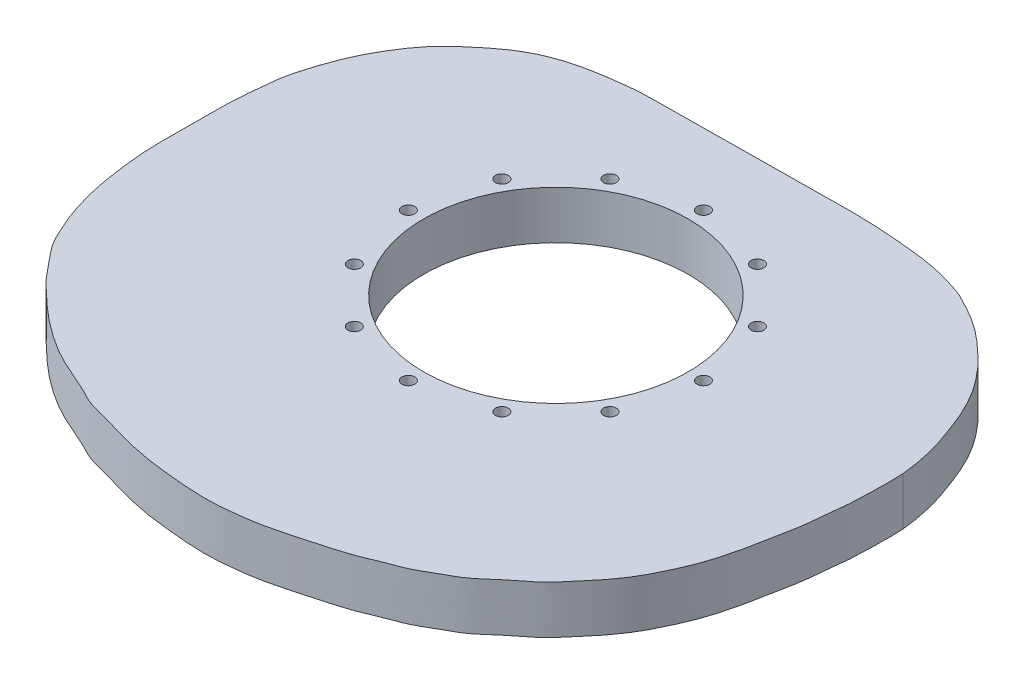
SolidWorks part; units mm, degrees
material "PC High Viscosity"
ref_plane "Front Plane" through (0, 0, 0) normal (0, 0, 1) x (1, 0, 0)
ref_plane "Top Plane" through (0, 0, 0) normal (0, 1, 0) x (1, 0, 0)
ref_plane "Right Plane" through (0, 0, 0) normal (1, 0, 0) x (0, 0, -1)
ref_plane "Plane1" through (0, -5, 0) normal (0, -1, 0) x (1, 0, 0)
sketch "Sketch1" plane through (0, -5, 0) normal (0, -1, 0) x (1, 0, 0)
  line L0 (-553.4146, 21.431) -> (-553.4146, 113.672) construction
  line L1 (-553.4146, 21.431) -> (-453.7553, 21.431) construction
  circle A0 centre (-640.9481, 175.1125) radius 4.5 construction
  circle A1 centre (-701.6642, 122.5526) radius 4.5 construction
  circle A2 centre (-720.0364, 42.0554) radius 4.5 construction
  circle A3 centre (-703.4746, -33.9322) radius 4.5 construction
  circle A4 centre (-640.0771, -82.4235) radius 4.5 construction
  circle A5 centre (-550.8446, -84.6039) radius 4.5 construction
  circle A6 centre (-463.1234, -82.9904) radius 4.5 construction
  circle A7 centre (-402.2158, -32.3116) radius 4.5 construction
  circle A8 centre (-390.2401, 53.8738) radius 4.5 construction
  circle A9 centre (-420.5023, 130.1207) radius 4.5 construction
  circle A10 centre (-489.4438, 179.9192) radius 4.5 construction
  circle A11 centre (-561.1968, 193.8588) radius 4.5 construction
  circle A12 centre (-553.4146, 21.431) radius 85 construction
  circle A13 centre (-553.4146, 21.431) radius 70.0278
  circle A14 centre (-553.4146, 21.431) radius 78.0278 construction
  circle A15 centre (-553.4146, -56.5968) radius 3.175 construction
  circle A16 centre (-592.4285, -46.143) radius 3.175 construction
  circle A17 centre (-620.9886, -17.5829) radius 3.175 construction
  circle A18 centre (-631.4424, 21.431) radius 3.175 construction
  circle A19 centre (-620.9886, 60.4449) radius 3.175 construction
  circle A20 centre (-592.4285, 89.0051) radius 3.175 construction
  circle A21 centre (-553.4146, 99.4588) radius 3.175 construction
  circle A22 centre (-514.4007, 89.0051) radius 3.175 construction
  circle A23 centre (-485.8405, 60.4449) radius 3.175 construction
  circle A24 centre (-475.3868, 21.431) radius 3.175 construction
  circle A25 centre (-485.8405, -17.5829) radius 3.175 construction
  circle A26 centre (-514.4007, -46.143) radius 3.175 construction
  circle A27 centre (-553.4146, 143.3336) radius 10 construction
  spline S0 degree 3 poles (-380.0492, 11.3845) (-380.3517, 7.6228) (-381.6942, -0.7552) (-384.4462, -11.6637) (-388.1031, -21.3921) (-391.9257, -31.5758) (-398.2955, -43.9247) (-407.1289, -55.652) (-416.3823, -64.7215) (-428.7027, -75.72) (-441.7653, -82.663) (-448.7361, -86.4746) (-459.3782, -89.3832) (-468.64, -91.8901) (-483.8831, -93.5312) (-505.2938, -95.3605) (-537.9356, -94.81) (-620.864, -94.0649) (-625.2898, -93.7427) (-632.6167, -93.1087) (-643.9696, -91.505) (-654.6984, -89.3136) (-665.5537, -85.8204) (-677.5449, -79.6796) (-689.8218, -69.7893) (-700.8189, -59.8464) (-709.7194, -47.179) (-717.4544, -32.8609) (-722.9168, -16.9365) (-725.8708, -5.4697) (-726.4326, 2.7477) (-728.0614, 15.9524) (-728.0166, 29.622) (-728.1832, 51.3785) (-728.2105, 66.1658) (-725.0161, 91.653) (-719.3074, 111.76) (-715.0325, 120.9389) (-713.403, 124.3556) knots 0.505449 0.505449 0.505449 0.505449 0.517879 0.529901 0.541289 0.553 0.566304 0.579903 0.592751 0.607328 0.620921 0.630996 0.642558 0.653666 0.667425 0.683271 0.705284 0.737162 0.74462 0.753697 0.76593 0.777787 0.789713 0.802766 0.81692 0.830645 0.844558 0.85902 0.87372 0.885805 0.895976 0.908692 0.922196 0.938566 0.952559 0.970499 0.987058 1 1 1 1
  spline S1 degree 3 poles (-713.403, 124.3556) (-712.0821, 127.125) (-709.6174, 132.1606) (-702.1703, 140.5425) (-695.5252, 149.3502) (-687.2231, 156.81) (-678.2069, 165.4785) (-664.3825, 175.5745) (-651.5938, 182.9116) (-634.0958, 189.8974) (-627.7186, 194.1731) (-612.1137, 197.5774) (-603.1302, 200.7835) (-587.8782, 204.2739) (-575.4184, 205.6622) (-564.4048, 206.8324) (-549.9761, 207.4282) (-539.5697, 206.291) (-527.523, 204.923) (-512.5859, 201.0346) (-500.8061, 197.7781) (-485.9282, 193.4712) (-475.4709, 188.5145) (-466.6222, 185.7658) (-457.1273, 179.7633) (-449.2856, 175.9256) (-442.2007, 170.2964) (-434.1418, 162.7727) (-425.2542, 156.6595) (-418.752, 148.5392) (-410.494, 139.3285) (-403.0006, 128.4908) (-397.6218, 117.6964) (-392.0423, 104.8055) (-388.9237, 93.1236) (-386.8542, 84.1236) (-385.1003, 73.5705) (-383.4988, 66.2151) (-382.2395, 58.9168) (-381.9359, 51.4349) (-380.4787, 42.1286) (-379.9782, 32.5082) (-379.8462, 20.9013) (-379.7802, 14.7308) (-380.0492, 11.3845) knots 0 0 0 0 0.010491 0.022303 0.034198 0.045974 0.058626 0.073219 0.08734 0.102444 0.112614 0.126407 0.137824 0.151733 0.164418 0.176314 0.189761 0.201308 0.213678 0.227608 0.240255 0.254221 0.266329 0.277135 0.288993 0.299529 0.310153 0.322011 0.333676 0.345096 0.357647 0.370545 0.382963 0.396339 0.408686 0.419576 0.431148 0.440987 0.450542 0.460302 0.471162 0.482342 0.494391 0.505449 0.505449 0.505449 0.505449
  spline S2 degree 3 poles (-416.048, 73.9534) (-415.1491, 69.9688) (-413.3544, 61.5127) (-410.2817, 50.6253) (-411.4639, 37.415) (-409.9353, 26.5066) (-411.4798, 13.3973) (-413.2696, 2.8643) (-415.1382, -9.0321) (-421.4323, -21.7111) (-425.0967, -33.4269) (-435.2379, -43.0196) (-442.4428, -50.8264) (-452.2717, -57.3134) (-462.4271, -61.9113) (-472.0745, -63.8466) (-484.0674, -66.7461) (-496.2163, -67.1856) (-506.8255, -67.2798) (-522.7494, -66.3115) (-538.215, -65.7687) (-552.65, -63.3169) (-572.2518, -63.1777) (-588.9265, -63.2549) (-602.7864, -63.0957) (-617.6834, -63.6358) (-628.0605, -61.835) (-641.4778, -61.4442) (-652.1162, -55.2219) (-662.1811, -50.8223) (-669.7824, -43.6164) (-678.7814, -34.3647) (-685.4941, -23.6234) (-690.2458, -13.857) (-695.8746, -5.4145) (-696.6763, 2.2451) (-699.3645, 9.541) (-700.0771, 17.2149) (-700.4267, 19.6406) (-700.4613, 21.3258) knots 0.497253 0.497253 0.497253 0.497253 0.511306 0.524668 0.538857 0.552096 0.566312 0.579288 0.592923 0.607749 0.621605 0.636124 0.649104 0.662576 0.675707 0.688086 0.701973 0.715679 0.728575 0.744324 0.759908 0.775045 0.792552 0.808757 0.82355 0.838636 0.851568 0.865817 0.879672 0.892648 0.905353 0.919565 0.933656 0.946771 0.959186 0.970008 0.98113 0.991857 1 1 1 1 construction
  spline S3 degree 3 poles (-700.4613, 21.3258) (-700.5131, 23.8504) (-700.121, 31.2742) (-701.5501, 37.9343) (-699.7405, 50.296) (-698.9412, 59.7576) (-696.6744, 74.6182) (-694.4641, 84.4038) (-691.6982, 93.6625) (-687.8006, 102.083) (-682.1515, 110.4895) (-675.5545, 117.9879) (-670.7167, 126.5299) (-661.7282, 133.3325) (-652.3103, 140.7388) (-642.5176, 147.4639) (-630.4218, 153.59) (-621.6855, 157.448) (-608.9688, 162.0223) (-597.5804, 165.6069) (-582.0745, 167.5096) (-567.9172, 167.3907) (-554.8951, 167.628) (-542.6594, 166.8109) (-529.6605, 166.4616) (-518.4155, 165.4134) (-505.5105, 162.8) (-491.7029, 157.4806) (-481.5048, 153.1571) (-472.7683, 147.8066) (-462.8278, 142.6438) (-457.1543, 137.102) (-450.1152, 132.3365) (-444.3829, 127.2585) (-440.0707, 121.5018) (-433.954, 113.1249) (-428.3313, 105.4574) (-424.2878, 98.0882) (-418.6786, 85.1184) (-416.913, 77.7876) (-416.048, 73.9534) knots 0 0 0 0 0.012199 0.022882 0.036471 0.049062 0.064236 0.076941 0.089054 0.101091 0.113653 0.126137 0.138409 0.151591 0.165278 0.179039 0.193444 0.205808 0.220123 0.23395 0.249478 0.264472 0.278661 0.292545 0.306741 0.320005 0.334359 0.34961 0.362741 0.375417 0.388556 0.39971 0.411169 0.422021 0.432609 0.445369 0.457507 0.469012 0.48373 0.497253 0.497253 0.497253 0.497253 construction
  point P30 (-557.5221, -63.4696)
  point P62 (-553.4146, 21.431)
  dimension "D1" = 170
  dimension "D2" = 9
  dimension "D3" = 140.0556
  dimension "D4" = 8
  dimension "D5" = 6.35
  dimension "D7" = 20
  dimension "D6" = 12
extrude "Boss-Extrude1" add sketch "Sketch1" against normal blind 25.4
hole_wizard "1/4 Clearance Hole1" [suppressed] positions "Sketch2" profile "Sketch3" hole size "1/4" standard "ANSI Inch"
sketch "Sketch2" plane through (0, -5, 0) normal (0, -1, 0) x (-1, 0, 0)
  point P0 (640.9481, -175.1125)
  point P3 (701.6642, -122.5526)
  point P6 (720.0364, -42.0554)
  point P9 (703.4746, 33.9322)
  point P12 (640.0771, 82.4235)
  point P15 (550.8446, 84.6039)
  point P18 (463.1234, 82.9904)
  point P21 (402.2158, 32.3116)
  point P24 (390.2401, -53.8738)
  point P27 (420.5023, -130.1207)
  point P30 (489.4438, -179.9192)
  point P33 (561.1968, -193.8588)
sketch "Sketch3" plane through (-640.9481, -5, 175.1125) normal (1, 0, 0) x (0, 0, -1)
  line L0 (0, 0) -> (0, 5)
  line L1 (0, 5) -> (3.3782, 5)
  line L2 (3.3782, 5) -> (3.3782, 0)
  line L5 (3.3782, 0) -> (0, 0)
  line L11 (0, -6.35) -> (0, 107.95) construction
  dimension "Thru Hole Dia." = 6.7564
  dimension "Thru Hole Depth" = 5
hole_wizard "1/4 Clearance Hole2" positions "Sketch4" profile "Sketch6" hole size "1/4" standard "ANSI Inch" end condition through all
sketch "Sketch4" plane through (0, -5, 0) normal (0, -1, 0) x (-1, 0, 0)
  point P0 (592.4285, -89.0051)
  point P3 (620.9886, -60.4449)
  point P6 (631.4424, -21.431)
  point P9 (620.9886, 17.5829)
  point P12 (592.4285, 46.143)
  point P15 (553.4146, 56.5968)
  point P18 (514.4007, 46.143)
  point P21 (485.8405, 17.5829)
  point P24 (475.3868, -21.431)
  point P27 (485.8405, -60.4449)
  point P30 (514.4007, -89.0051)
  point P33 (553.4146, -99.4588)
sketch "Sketch6" plane through (-592.4285, -5, 89.0051) normal (1, 0, 0) x (0, 0, -1)
  line L0 (0, 0) -> (0, 25.4)
  line L1 (0, 25.4) -> (3.3782, 25.4)
  line L2 (3.3782, 25.4) -> (3.3782, 0)
  line L5 (3.3782, 0) -> (0, 0)
  line L11 (0, -6.35) -> (0, 107.95) construction
  dimension "Thru Hole Dia." = 6.7564
  dimension "Thru Hole Depth" = 25.4
hole_wizard "M20x1.5 Tapped Hole1" [suppressed] positions "Sketch7" profile "Sketch8" tap size "M20x1.5" standard "ANSI Metric"
sketch "Sketch7" plane through (0, -5, 0) normal (0, -1, 0) x (-1, 0, 0)
  point P0 (553.4146, -143.3336)
sketch "Sketch8" plane through (-553.4146, -5, 143.3336) normal (1, 0, 0) x (0, 0, -1)
  line L0 (0, 0) -> (0, 5)
  line L1 (0, 5) -> (9.25, 5)
  line L2 (9.25, 5) -> (9.25, 0)
  line L5 (9.25, 0) -> (0, 0)
  line L11 (0, -6.35) -> (0, 107.95) construction
  dimension "Thru Tap Drill Dia." = 18.5
  dimension "Thru Tap Drill Depth" = 5
cosmetic thread "Hole Thread1" [suppressed] parameters "D2"=20
